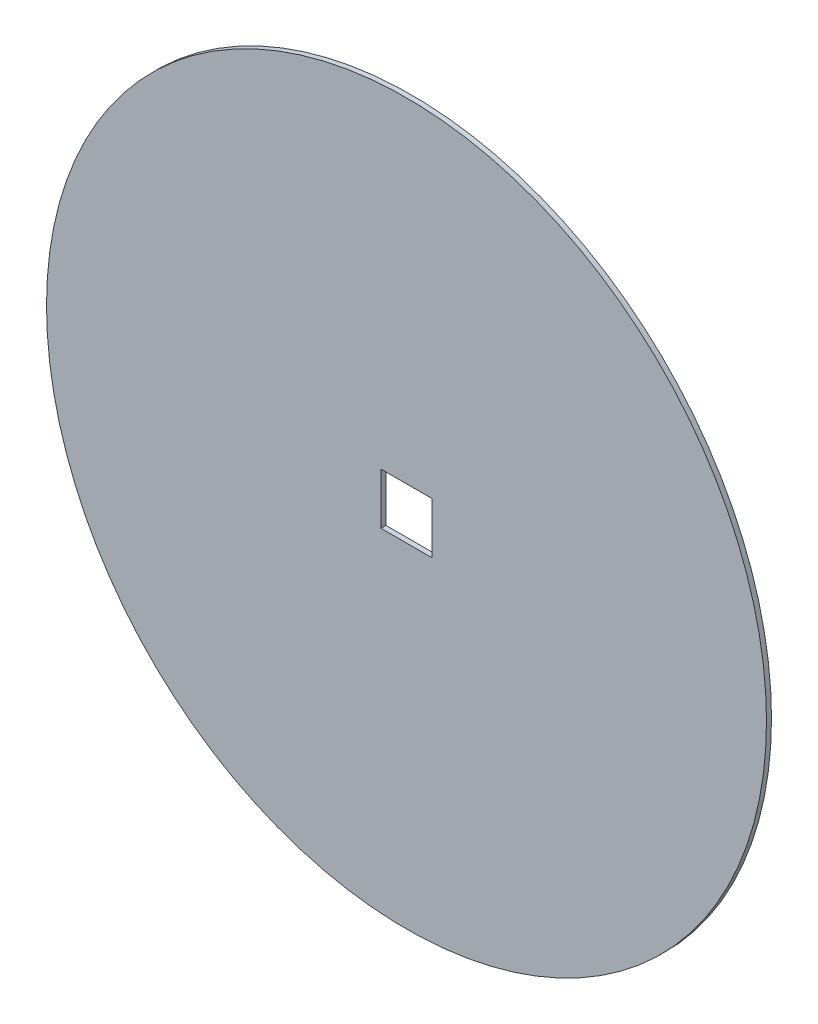
SolidWorks part; units mm, degrees
ref_plane "Front Plane" through (0, 0, 0) normal (0, 0, 1) x (1, 0, 0)
ref_plane "Top Plane" through (0, 0, 0) normal (0, 1, 0) x (1, 0, 0)
ref_plane "Right Plane" through (0, 0, 0) normal (1, 0, 0) x (0, 0, -1)
sketch "Sketch1" plane through (0, 0, 0) normal (0, 0, 1) x (1, 0, 0)
  line L1 (-10.25, 10.25) -> (10.25, 10.25)
  line L2 (-10.25, 10.25) -> (-10.25, -10.25)
  line L3 (-10.25, -10.25) -> (10.25, -10.25)
  line L4 (10.25, 10.25) -> (10.25, -10.25)
  line L5 (-10.25, 10.25) -> (10.25, -10.25) construction
  line L6 (-10.25, -10.25) -> (10.25, 10.25) construction
  circle A0 centre (0, 0) radius 144
  dimension "D1" = 288
  dimension "D2" = 20.5
  dimension "D3" = 20.5
extrude "Boss-Extrude1" add sketch "Sketch1" along normal blind 2
